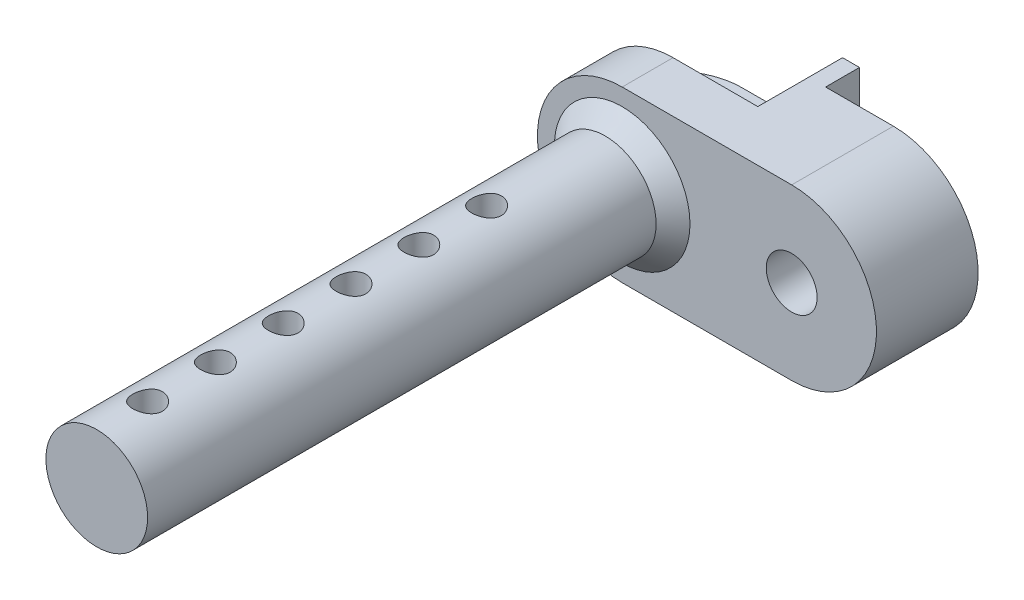
SolidWorks part; units mm, degrees
ref_plane "Přední rovina" through (0, 0, 0) normal (0, 0, 1) x (1, 0, 0)
ref_plane "Horní rovina" through (0, 0, 0) normal (0, 1, 0) x (1, 0, 0)
ref_plane "Pravá rovina" through (0, 0, 0) normal (1, 0, 0) x (0, 0, -1)
sketch "Skica1" plane through (0, 0, 0) normal (0, 0, 1) x (1, 0, 0)
  line L0 (0, 0) -> (10, 0)
  line L1 (0, -10) -> (10, -10)
  arc A0 (0, 0) -> (0, -10) centre (0, -5) ccw
  arc A1 (10, 0) -> (10, -10) centre (10, -5) cw
  dimension "D2" = 10
  dimension "D1" = 10
extrude "Vysunout1" add sketch "Skica1" along normal blind 8
sketch "Skica2" plane through (0, 0, 8) normal (0, 0, 1) x (1, 0, 0)
  circle A0 centre (0, -5) radius 3
  arc A1 (0, 0) -> (0, -10) centre (0, -5) ccw construction
  dimension "D1" = 6
extrude "Vysunout2" add sketch "Skica2" along normal blind 31
hole_wizard "M3 závitové díry1" positions "Skica4" profile "Skica3" tap size "M3" standard "ISO" end condition through all
sketch "Skica4" plane through (0, 0, 8) normal (0, 0, 1) x (1, 0, 0)
  arc A0 (10, -10) -> (10, 0) centre (10, -5) ccw construction
  point P0 (10, -5)
sketch "Skica3" plane through (10, -5, 8) normal (1, 0, 0) x (0, -1, 0)
  line L0 (0, 0) -> (0, 8)
  line L1 (0, 8) -> (1.5, 8)
  line L2 (1.5, 8) -> (1.5, 0)
  line L5 (1.5, 0) -> (0, 0)
  line L11 (0, -6.35) -> (0, 107.95) construction
  dimension "Vnější průměr závitu" = 3
  dimension "Hloubka závitníku" = 8
chamfer "Zkosit1" distance 1 angle 45 1 edges at (3, -5, 8)
sketch "Skica5" plane through (0, 0, 0) normal (0, 0, -1) x (-1, 0, 0)
  line L1 (-16.5331, 1.8936) -> (-6, 1.8936)
  line L2 (-16.5331, 1.8936) -> (-16.5331, -11.7437)
  line L3 (-16.5331, -11.7437) -> (-6, -11.7437)
  line L4 (-6, 1.8936) -> (-6, -11.7437)
  arc A0 (-10, 0) -> (-10, -10) centre (-10, -5) ccw construction
  dimension "D1" = 4
extrude "Odebrat vysunutím1" cut sketch "Skica5" against normal blind 2
sketch "Skica6" plane through (0, 0, 2) normal (0, 0, -1) x (-1, 0, 0)
  line L0 (-6, -1) -> (-6, -9)
  line L1 (-6, -1) -> (-10, -1)
  line L2 (-6, -9) -> (-10, -9)
  line L4 (-6, -10) -> (-6, 0) construction
  line L5 (-6, 0) -> (-10, 0) construction
  arc A0 (-10, -1) -> (-10, -9) centre (-10, -5) ccw
  arc A1 (-10, 0) -> (-10, -10) centre (-10, -5) ccw construction
  dimension "D1" = 1
extrude "Odebrat vysunutím2" cut sketch "Skica6" against normal blind 2
sketch "Skica7" plane through (0, 0, 0) normal (0, 0, -1) x (-1, 0, 0)
  line L0 (-10, -5) -> (5.5973, -5) construction
  line L1 (-6, -10) -> (-6, 0) construction
  line L2 (-5, 1.0663) -> (5.5973, 1.0663)
  line L3 (-5, 1.0663) -> (-5, -4.5)
  line L4 (-5, -4.5) -> (5.5973, -4.5)
  line L5 (5.5973, 1.0663) -> (5.5973, -4.5)
  line L6 (5.5973, -11.0663) -> (5.5973, -5.5)
  line L7 (-5, -5.5) -> (5.5973, -5.5)
  line L8 (-5, -11.0663) -> (-5, -5.5)
  line L9 (-5, -11.0663) -> (5.5973, -11.0663)
  dimension "D1" = 1
  dimension "D2" = 1
extrude "Odebrat vysunutím3" cut sketch "Skica7" against normal blind 5
fillet "Zaoblit1" radius 4 1 edges at (-5, -5, 0)
ref_plane "Rovina1" through (0, -8, 0) normal (0, 1, 0) x (-1, 0, 0)
sketch "Skica8" plane through (0, -8, 0) normal (0, 1, 0) x (-1, 0, 0)
  line L0 (0, 39) -> (0, 9) construction
  line L1 (3, 39) -> (-3, 39) construction
  line L2 (0, 53.931) -> (0, 18.069) construction
  circle A0 centre (0, 36) radius 0.875
  dimension "D1" = 1.75
  dimension "D2" = 3
extrude "Odebrat vysunutím4" cut sketch "Skica8" along normal blind 6
pattern_linear "LinPole1" count 6 spacing 4 along (0, 0, -1) count 4 spacing 50 along (0, 0, -1) of "Odebrat vysunutím4"
